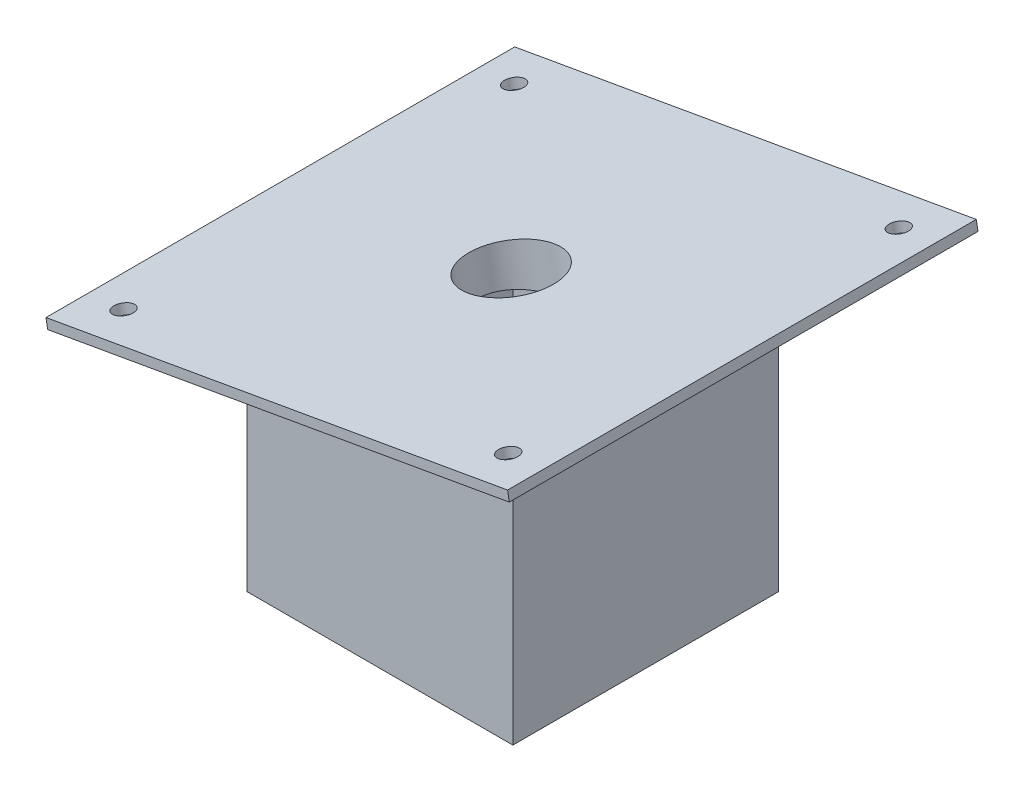
SolidWorks part; units mm, degrees
ref_plane "Front Plane" through (0, 0, 0) normal (0, 0, 1) x (1, 0, 0)
ref_plane "Top Plane" through (0, 0, 0) normal (0, 1, 0) x (1, 0, 0)
ref_plane "Right Plane" through (0, 0, 0) normal (1, 0, 0) x (0, 0, -1)
sketch "Sketch1" plane through (0, 0, 0) normal (0, 1, 0) x (1, 0, 0)
  line L1 (-43.18, 43.18) -> (43.18, 43.18)
  line L2 (-43.18, 43.18) -> (-43.18, -43.18)
  line L3 (-43.18, -43.18) -> (43.18, -43.18)
  line L4 (43.18, 43.18) -> (43.18, -43.18)
  line L5 (-43.18, 43.18) -> (43.18, -43.18) construction
  line L6 (-43.18, -43.18) -> (43.18, 43.18) construction
  point P0 (0, 0)
  dimension "D1" = 86.36
extrude "Boss-Extrude1" add sketch "Sketch1" along normal blind 95.25
sketch "Sketch2" plane through (0, 0, 0) normal (0, -1, 0) x (-1, 0, 0)
  line L1 (39.37, -39.37) -> (-39.37, -39.37)
  line L2 (39.37, -39.37) -> (39.37, 39.37)
  line L3 (39.37, 39.37) -> (-39.37, 39.37)
  line L4 (-39.37, -39.37) -> (-39.37, 39.37)
  line L5 (39.37, -39.37) -> (-39.37, 39.37) construction
  line L6 (39.37, 39.37) -> (-39.37, -39.37) construction
  point P0 (0, 0)
  dimension "D1" = 78.74
extrude "Cut-Extrude1" cut sketch "Sketch2" against normal blind 76.2
sketch "Sketch4" plane through (0, 0, -43.18) normal (0, 0, -1) x (-1, 0, 0)
  line L0 (-43.18, 95.25) -> (43.18, 80.0224)
  line L1 (43.18, 95.25) -> (43.18, 0) construction
  line L2 (43.18, 80.0224) -> (43.18, 95.25)
  line L3 (43.18, 95.25) -> (-43.18, 95.25)
  dimension "D1" = 10
extrude "Cut-Extrude2" cut sketch "Sketch4" against normal through all
ref_plane "Plane2" through (-14.9867, 84.9936, 0) normal (-0.1736, 0.9848, 0) x (0.9848, 0.1736, 0)
sketch "Sketch7" plane through (-14.9867, 84.9936, 0) normal (-0.1736, 0.9848, 0) x (0.9848, 0.1736, 0)
  line L0 (59.064, 0) -> (-28.6283, 0) construction
  line L1 (-60.9821, 76.2) -> (91.4179, 76.2)
  line L2 (-60.9821, 76.2) -> (-60.9821, -76.2)
  line L3 (-60.9821, -76.2) -> (91.4179, -76.2)
  line L4 (91.4179, 76.2) -> (91.4179, -76.2)
  line L5 (-60.9821, 76.2) -> (91.4179, -76.2) construction
  line L6 (-60.9821, -76.2) -> (91.4179, 76.2) construction
  point P0 (15.2179, 0)
  dimension "D1" = 152.4
sketch "Sketch8" plane through (-14.9867, 84.9936, 0) normal (-0.1736, 0.9848, 0) x (0.9848, 0.1736, 0)
  line L0 (59.064, 0) -> (-28.6283, 0) construction
  line L1 (59.064, -43.18) -> (59.064, 43.18) construction
  line L2 (-28.6283, -43.18) -> (-28.6283, 43.18) construction
  line L3 (15.2179, -43.18) -> (15.2179, 43.18) construction
  line L4 (59.064, -43.18) -> (-28.6283, -43.18) construction
  line L5 (59.064, 43.18) -> (-28.6283, 43.18) construction
extrude "Boss-Extrude2" add sketch "Sketch7" along normal blind 3.175
sketch "Sketch9" plane through (-15.538, 88.1204, 0) normal (-0.1736, 0.9848, 0) x (0.9848, 0.1736, 0)
  line L0 (15.2179, -43.18) -> (15.2179, 43.18) construction
  circle A0 centre (15.2179, 0) radius 13.97
extrude "Cut-Extrude4" cut sketch "Sketch9" against normal through all
hole_wizard "1/4 (0.25) Diameter Hole1" positions "Sketch13" profile "Sketch14" hole size "1/4" standard "ANSI Inch"
sketch "Sketch13" plane through (-15.538, 88.1204, 0) normal (-0.1736, 0.9848, 0) x (0.9848, 0.1736, 0)
  line L0 (-48.2821, 63.5) -> (78.7179, 63.5) construction
  line L1 (78.7179, 63.5) -> (78.7179, -63.5) construction
  line L2 (78.7179, -63.5) -> (-48.2821, -63.5) construction
  line L3 (-48.2821, -63.5) -> (-48.2821, 63.5) construction
  line L5 (-60.9821, 76.2) -> (-60.9821, -76.2) construction
  line L6 (91.4179, 76.2) -> (-60.9821, 76.2) construction
  line L7 (-60.9821, -76.2) -> (91.4179, -76.2) construction
  line L8 (91.4179, -76.2) -> (91.4179, 76.2) construction
  point P0 (-48.2821, 63.5)
  point P2 (78.7179, 63.5)
  point P4 (78.7179, -63.5)
  point P6 (-48.2821, -63.5)
  point P23 (-42.4192, -40.1177)
  point P26 (46.8279, 79.8345)
  dimension "D1" = 127
  dimension "D2" = 12.7
  dimension "D3" = 12.7
sketch "Sketch14" plane through (-63.0866, 79.7363, -63.5) normal (0, 0, 1) x (-0.9848, -0.1736, 0)
  line L0 (0, 0) -> (0, 5.0827)
  line L1 (0, 5.0827) -> (3.175, 3.175)
  line L2 (3.175, 3.175) -> (3.175, 0)
  line L5 (3.175, 0) -> (0, 0)
  line L10 (0, 5.0827) -> (-3.175, 3.175) construction
  line L11 (0, -6.35) -> (0, 107.95) construction
  dimension "Hole Dia." = 6.35
  dimension "Hole Depth" = 3.175
  dimension "Drill Angle" = 118
